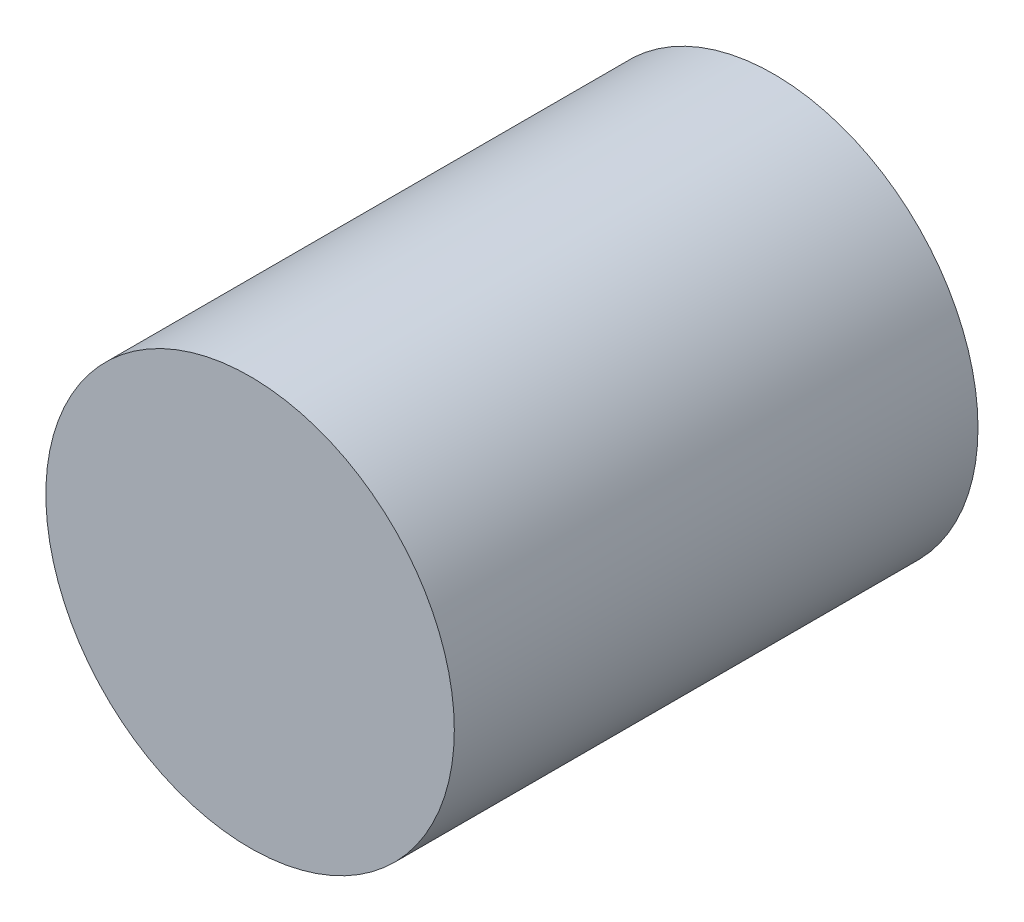
SolidWorks part; units mm, degrees
ref_plane "Front Plane" through (0, 0, 0) normal (0, 0, 1) x (1, 0, 0)
ref_plane "Top Plane" through (0, 0, 0) normal (0, 1, 0) x (1, 0, 0)
ref_plane "Right Plane" through (0, 0, 0) normal (1, 0, 0) x (0, 0, -1)
sketch "Sketch1" plane through (0, 0, 0) normal (0, 0, 1) x (1, 0, 0)
  circle A0 centre (0, 0) radius 9.906
  dimension "D1" = 19.812
extrude "Boss-Extrude1" add sketch "Sketch1" along normal blind 25.4
